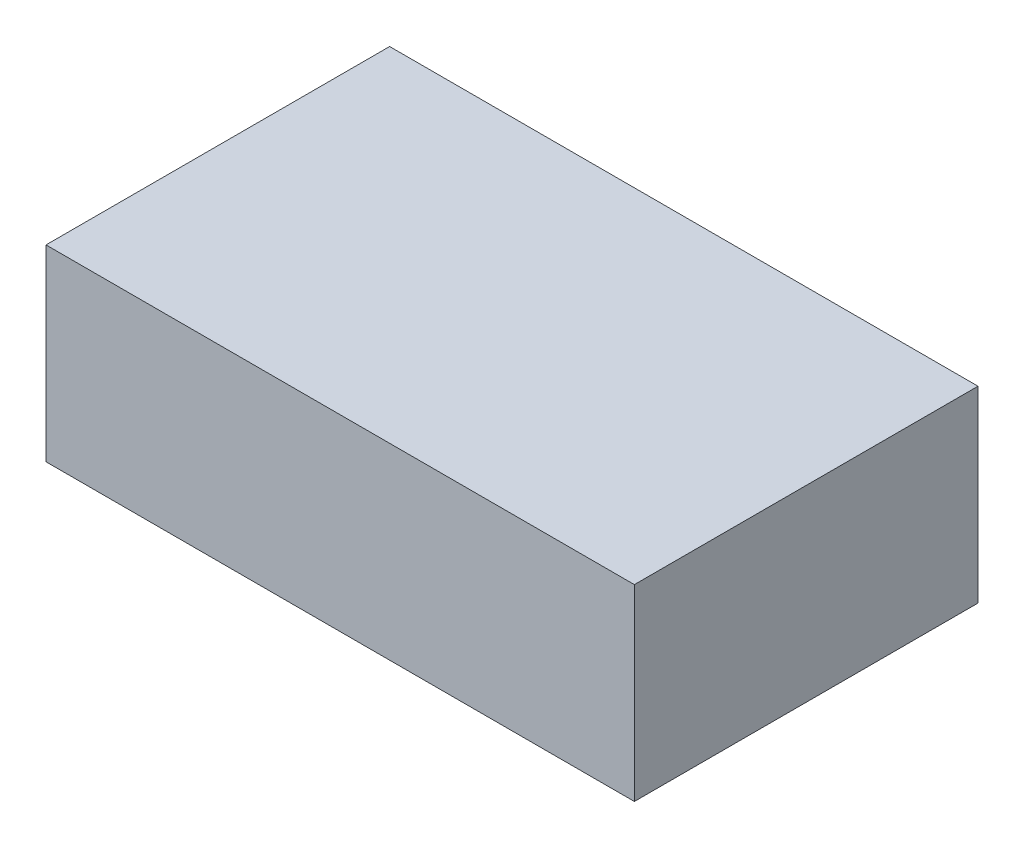
SolidWorks part; units mm, degrees
ref_plane "Front Plane" through (0, 0, 0) normal (0, 0, 1) x (1, 0, 0)
ref_plane "Top Plane" through (0, 0, 0) normal (0, 1, 0) x (1, 0, 0)
ref_plane "Right Plane" through (0, 0, 0) normal (1, 0, 0) x (0, 0, -1)
sketch "Sketch1" plane through (0, 0, 0) normal (0, 1, 0) x (1, 0, 0)
  line L1 (-53.25, -31.1) -> (53.25, -31.1)
  line L2 (-53.25, -31.1) -> (-53.25, 31.1)
  line L3 (-53.25, 31.1) -> (53.25, 31.1)
  line L4 (53.25, -31.1) -> (53.25, 31.1)
  line L5 (-53.25, -31.1) -> (53.25, 31.1) construction
  line L6 (-53.25, 31.1) -> (53.25, -31.1) construction
  point P0 (0, 0)
  dimension "D1" = 62.2
  dimension "D2" = 106.5
extrude "Boss-Extrude1" add sketch "Sketch1" along normal blind 34
